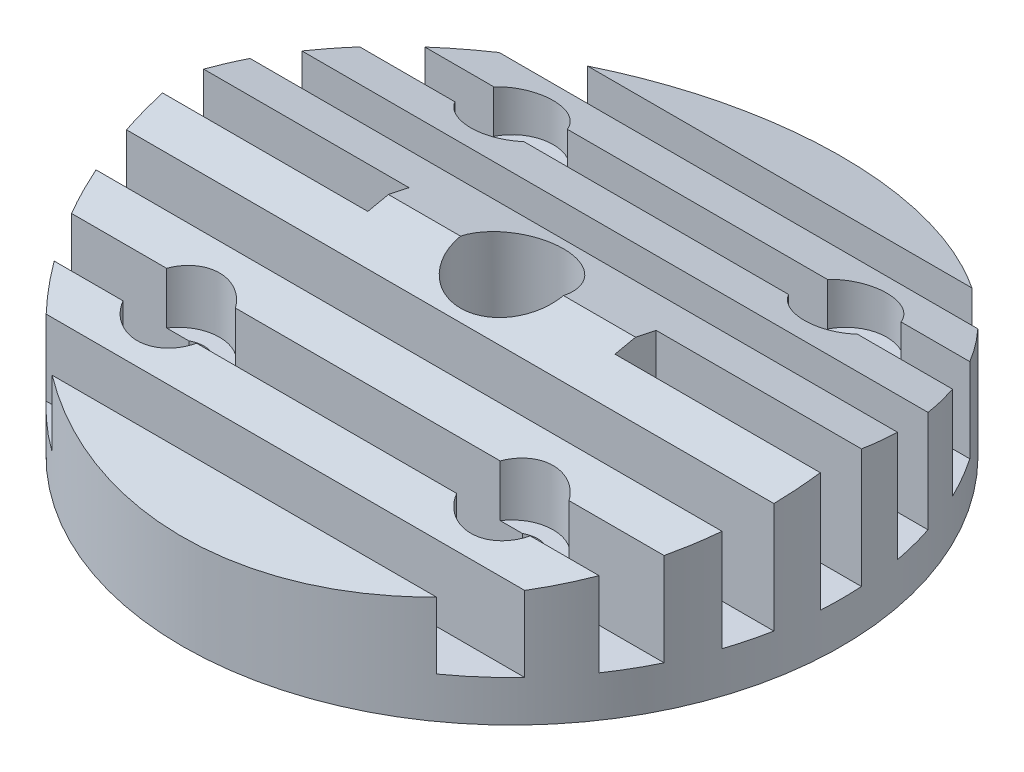
SolidWorks part; units mm, degrees
ref_plane "Front Plane" through (0, 0, 0) normal (0, 0, 1) x (1, 0, 0)
ref_plane "Top Plane" through (0, 0, 0) normal (0, 1, 0) x (1, 0, 0)
ref_plane "Right Plane" through (0, 0, 0) normal (1, 0, 0) x (0, 0, -1)
sketch "Sketch2" plane through (0, 0, 0) normal (0, 1, 0) x (1, 0, 0)
  circle A0 centre (0, 0) radius 16
  dimension "D1" = 32
extrude "Boss-Extrude1" add sketch "Sketch2" along normal blind 8
sketch "Sketch3" plane through (0, 8, 0) normal (0, 1, 0) x (1, 0, 0)
  line L0 (0, 0) -> (28.8034, 0) construction
  line L1 (14.418, -13) -> (14.418, -11)
  line L2 (-18.7513, 5) -> (18.406, 5)
  line L3 (-18.7513, 5) -> (-18.7513, 3)
  line L4 (-18.7513, 3) -> (18.406, 3)
  line L5 (18.406, 5) -> (18.406, 3)
  line L6 (-17.4511, 9) -> (16.2416, 9)
  line L7 (-17.4511, 9) -> (-17.4511, 7)
  line L8 (-17.4511, 7) -> (16.2416, 7)
  line L9 (16.2416, 9) -> (16.2416, 7)
  line L10 (-13.2068, 13) -> (14.418, 13)
  line L11 (-13.2068, 13) -> (-13.2068, 11)
  line L12 (-13.2068, 11) -> (14.418, 11)
  line L13 (14.418, 13) -> (14.418, 11)
  line L14 (-13.2068, -11) -> (14.418, -11)
  line L15 (-13.2068, -13) -> (-13.2068, -11)
  line L16 (-13.2068, -13) -> (14.418, -13)
  line L17 (16.2416, -9) -> (16.2416, -7)
  line L18 (-17.4511, -7) -> (16.2416, -7)
  line L19 (-17.4511, -9) -> (-17.4511, -7)
  line L20 (-17.4511, -9) -> (16.2416, -9)
  line L21 (18.406, -5) -> (18.406, -3)
  line L22 (-18.7513, -3) -> (18.406, -3)
  line L23 (-18.7513, -5) -> (-18.7513, -3)
  line L24 (-18.7513, -5) -> (18.406, -5)
  line L25 (0, 0) -> (0, 18.5628) construction
  line L26 (-18.7513, 1) -> (-6, 1)
  line L27 (-18.7513, 1) -> (-18.7513, -1)
  line L28 (-18.7513, -1) -> (-6, -1)
  line L29 (-6, 1) -> (-6, -1)
  line L30 (6, 1) -> (6, -1)
  line L31 (18.7513, -1) -> (6, -1)
  line L32 (18.7513, 1) -> (18.7513, -1)
  line L33 (18.7513, 1) -> (6, 1)
  dimension "D1" = 3
  dimension "D2" = 2
  dimension "D3" = 2
  dimension "D4" = 2
  dimension "D5" = 2
  dimension "D6" = 2
  dimension "D7" = 2
  dimension "D8" = 6
extrude "Cut-Extrude1" cut sketch "Sketch3" against normal blind 6
sketch "Sketch4" plane through (0, 8, 0) normal (0, 1, 0) x (1, 0, 0)
  circle A0 centre (0, 0) radius 2.5
  dimension "D1" = 5
extrude "Cut-Extrude2" cut sketch "Sketch4" against normal blind 4
hole_wizard "Tap Drill for M3x0.5 Tap1" positions "Sketch7" profile "Sketch6" hole size "M3x0.5" standard "ANSI Metric"
sketch "Sketch7" plane through (0, 0, 0) normal (0, -1, 0) x (-1, 0, 0)
  point P0 (0, 0)
sketch "Sketch6" plane through (0, 0, 0) normal (1, 0, 0) x (0, 0, -1)
  line L0 (0, 0) -> (0, 6.2511)
  line L1 (0, 6.2511) -> (1.25, 5.5)
  line L2 (1.25, 5.5) -> (1.25, 0)
  line L5 (1.25, 0) -> (0, 0)
  line L10 (0, 6.2511) -> (-1.25, 5.5) construction
  line L11 (0, -6.35) -> (0, 107.95) construction
  dimension "Hole Dia." = 2.5
  dimension "Hole Depth" = 5.5
  dimension "Drill Angle" = 118
sketch "Sketch8" plane through (0, 0, 0) normal (0, -1, 0) x (1, 0, 0)
  circle A0 centre (0, 0) radius 9
  circle A1 centre (0, 0) radius 8
  dimension "D1" = 18
  dimension "D2" = 1
extrude "Boss-Extrude2" add sketch "Sketch8" along normal blind 0.5
hole_wizard "CBORE for M4 Pan Head Machine Screw1" positions "Sketch11" profile "Sketch10" counterbore size "M4" standard "ANSI Metric" end condition up to next
sketch "Sketch11" plane through (0, 8, 0) normal (0, 1, 0) x (1, 0, 0)
  line L0 (0, 0) -> (-21.218, 0) construction
  line L2 (0, 0) -> (-15.7968, -15.7968) construction
  line L4 (0, 0) -> (0, -19.2217) construction
  point P0 (-8.1, -8.1)
  dimension "D1" = 45
  dimension "D2" = 8.1
  dimension "D3" = 8.1
sketch "Sketch10" plane through (-8.1, 8, 8.1) normal (1, 0, 0) x (0, 0, 1)
  line L0 (0, 0) -> (0, 8.001)
  line L1 (0, 8.001) -> (1.25, 8.001)
  line L3 (1.25, 8.001) -> (1.25, 4)
  line L4 (1.25, 4) -> (2, 4)
  line L5 (2, 4) -> (2, 0)
  line L7 (2, 0) -> (0, 0)
  line L11 (0, -6.35) -> (0, 107.95) construction
  dimension "Thru Hole Dia." = 2.5
  dimension "Thru Hole Depth" = 8.001
  dimension "C'Bore Dia." = 4
  dimension "C'Bore Depth" = 4
pattern_circular "CirPattern1" count 4 over 360 about axis through (0, 0, 0) along (0, 1, 0) of "CBORE for M4 Pan Head Machine Screw1"
sketch "Sketch12" plane through (0, 0, 0) normal (1, 0, 0) x (0, 0, -1)
  line L0 (0, 12.094) -> (0, -4.4252) construction
  line L1 (0, 8) -> (16, 8)
  line L2 (1, 8) -> (-1, 8) construction
  line L3 (0, 8) -> (17.0324, 4.3797)
  line L4 (17.0324, 4.3797) -> (17.0324, 8)
  line L5 (17.0324, 8) -> (16, 8)
  dimension "D1" = 12
extrude "Cut-Extrude3" cut sketch "Sketch12" against normal mid plane 40.5
mirror "Mirror1" about plane through (0, 0, 0) normal (0, 0, 1) of "Cut-Extrude3"
